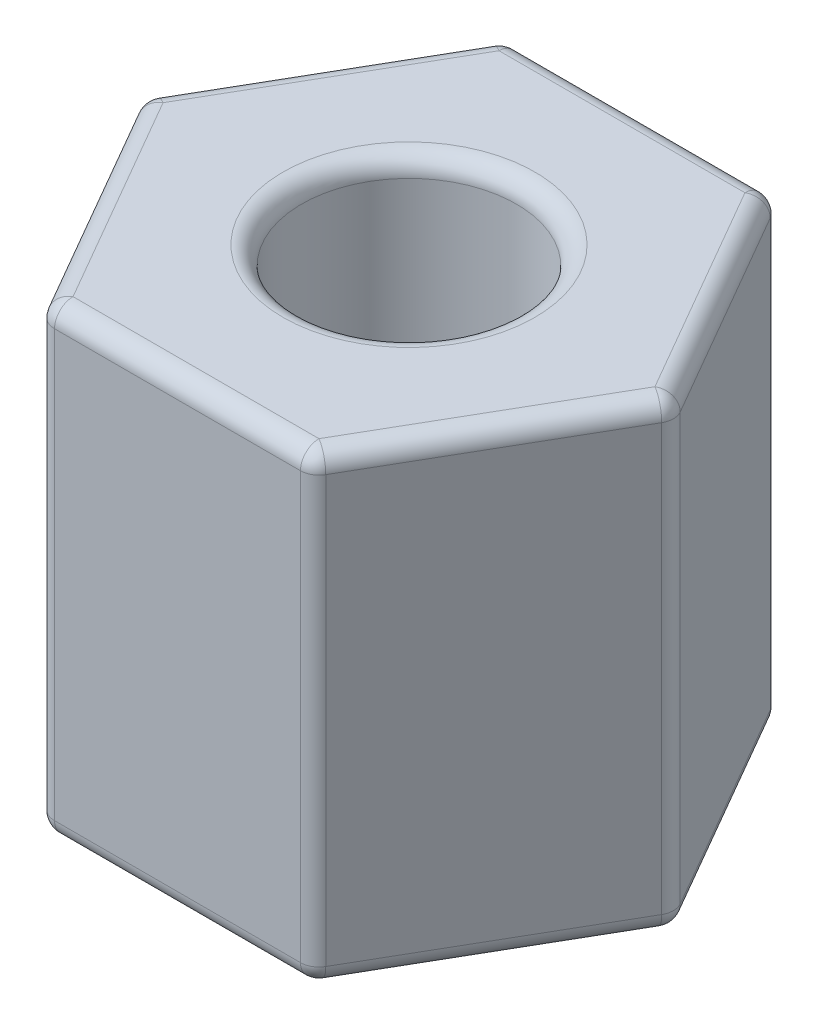
SolidWorks part; units mm, degrees
material "1060 Alloy"
ref_plane "Front Plane" through (0, 0, 0) normal (0, 0, 1) x (1, 0, 0)
ref_plane "Top Plane" through (0, 0, 0) normal (0, 1, 0) x (1, 0, 0)
ref_plane "Right Plane" through (0, 0, 0) normal (1, 0, 0) x (0, 0, -1)
sketch "Sketch1" plane through (0, 0, 0) normal (0, 1, 0) x (1, 0, 0)
  line L1 (1.8331, -3.175) -> (3.6662, 0)
  line L2 (3.6662, 0) -> (1.8331, 3.175)
  line L3 (1.8331, 3.175) -> (-1.8331, 3.175)
  line L4 (-1.8331, 3.175) -> (-3.6662, 0)
  line L5 (-3.6662, 0) -> (-1.8331, -3.175)
  line L6 (-1.8331, -3.175) -> (1.8331, -3.175)
  circle A0 centre (0, 0) radius 3.175 construction
  circle A1 centre (0, 0) radius 1.4732
  dimension "D2" = 2.9464
  dimension "D1" = 6.35
extrude "Boss-Extrude1" add sketch "Sketch1" along normal blind 6.35
fillet "Fillet1" radius 0.254 20 edges at (0, 6.35, 1.4732) (0, 0, 1.4732) (-2.7496, 0, -1.5875) (0, 0, -3.175) (2.7496, 0, -1.5875) (2.7496, 0, 1.5875) (0, 0, 3.175) (-2.7496, 0, 1.5875) (-1.8331, 3.175, 3.175) (-3.6662, 3.175, 0) (-1.8331, 3.175, -3.175) (1.8331, 3.175, -3.175) (3.6662, 3.175, 0) (1.8331, 3.175, 3.175) (2.7496, 6.35, -1.5875) (0, 6.35, -3.175) (-2.7496, 6.35, -1.5875) (-2.7496, 6.35, 1.5875) (0, 6.35, 3.175) (2.7496, 6.35, 1.5875)
